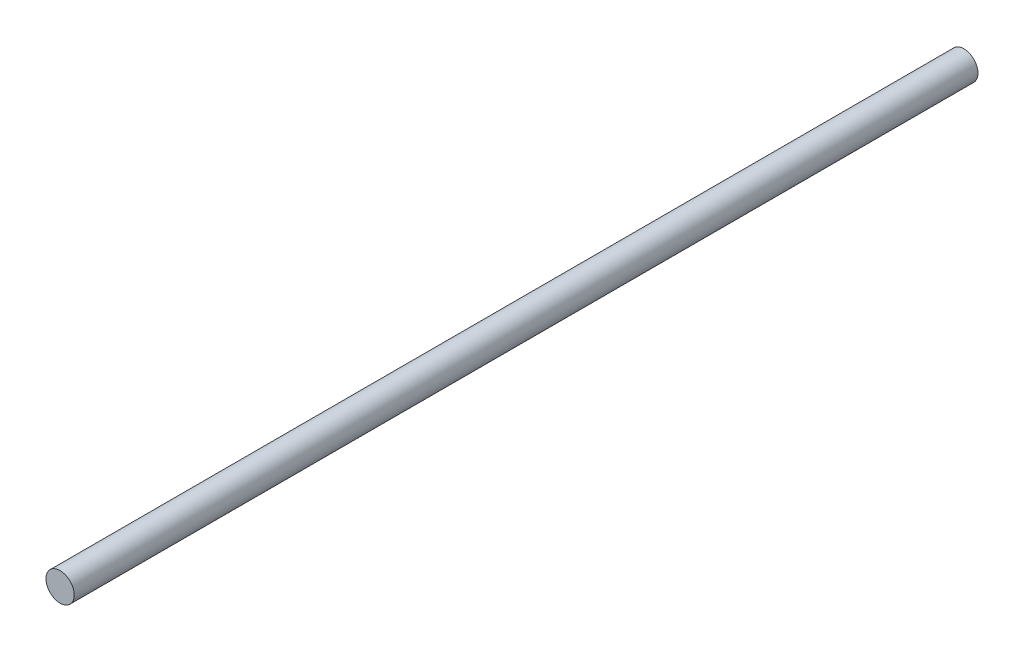
SolidWorks part; units mm, degrees
material "6063-T1"
ref_plane "Front Plane" through (0, 0, 0) normal (0, 0, 1) x (1, 0, 0)
ref_plane "Top Plane" through (0, 0, 0) normal (0, 1, 0) x (1, 0, 0)
ref_plane "Right Plane" through (0, 0, 0) normal (1, 0, 0) x (0, 0, -1)
sketch "Sketch1" plane through (0, 0, 0) normal (0, 0, 1) x (1, 0, 0)
  circle A0 centre (0, 0) radius 1.5
  dimension "D1" = 3
extrude "Boss-Extrude1" add sketch "Sketch1" along normal blind 96
